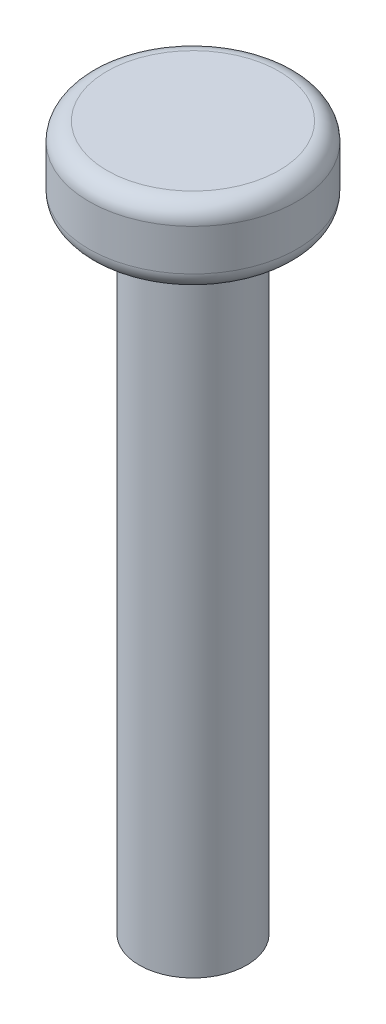
SolidWorks part; units mm, degrees
ref_plane "Спереди" through (0, 0, 0) normal (0, 0, 1) x (1, 0, 0)
ref_plane "Сверху" through (0, 0, 0) normal (0, 1, 0) x (1, 0, 0)
ref_plane "Справа" through (0, 0, 0) normal (1, 0, 0) x (0, 0, -1)
sketch "Sketch1" plane through (0, 0, 0) normal (0, 1, 0) x (1, 0, 0)
  circle A0 centre (0, 0) radius 3
  dimension "D1" = 6
extrude "Boss-Extrude1" add sketch "Sketch1" along normal blind 35
sketch "Sketch2" plane through (0, 35, 0) normal (0, 1, 0) x (1, 0, 0)
  circle A0 centre (0, 0) radius 5.8
  dimension "D1" = 11.6
extrude "Boss-Extrude2" add sketch "Sketch2" along normal blind 4.3
fillet "Fillet1" radius 1 2 edges at (0, 35, 5.8) (0, 39.3, 5.8)
